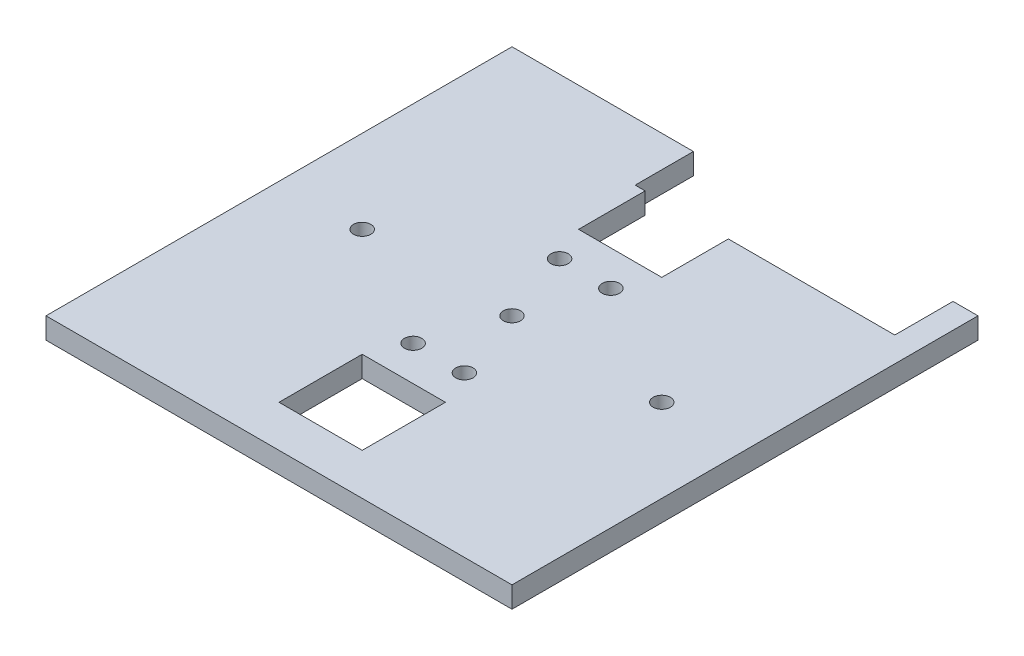
SolidWorks part; units mm, degrees
ref_plane "Front Plane" through (0, 0, 0) normal (0, 0, 1) x (1, 0, 0)
ref_plane "Top Plane" through (0, 0, 0) normal (0, 1, 0) x (1, 0, 0)
ref_plane "Right Plane" through (0, 0, 0) normal (1, 0, 0) x (0, 0, -1)
sketch "Sketch1" plane through (0, 0, 0) normal (0, 1, 0) x (1, 0, 0)
  line L1 (0, 0) -> (225, 0)
  line L2 (0, 0) -> (0, 225)
  line L3 (0, 225) -> (225, 225)
  line L4 (225, 0) -> (225, 225)
  line L5 (0, 0) -> (225, 225) construction
  line L6 (0, 225) -> (225, 0) construction
  point P4 (112.5, 112.5)
  dimension "D1" = 225
  dimension "D2" = 225
extrude "Boss-Extrude1" add sketch "Sketch1" along normal blind 6.35
sketch "Sketch2" plane through (0, 6.35, 0) normal (0, 1, 0) x (1, 0, 0)
  line L0 (222.5, 222.5) -> (222.5, 225) construction
  line L1 (2.5, 2.5) -> (222.5, 2.5) construction
  line L2 (2.5, 2.5) -> (2.5, 222.5) construction
  line L3 (2.5, 222.5) -> (222.5, 222.5) construction
  line L4 (222.5, 2.5) -> (222.5, 222.5) construction
  line L5 (112.5, 222.5) -> (112.5, 2.5) construction
  line L6 (2.5, 112.5) -> (222.5, 112.5) construction
  line L7 (225, 225) -> (0, 225) construction
  line L8 (222.5, 222.5) -> (225, 222.5) construction
  line L9 (225, 0) -> (225, 225) construction
  line L10 (2.5, 2.5) -> (0, 2.5) construction
  line L11 (0, 225) -> (0, 0) construction
  line L12 (2.5, 2.5) -> (2.5, 0) construction
  line L13 (0, 0) -> (225, 0) construction
  circle A0 centre (216.74, 216.74) radius 1.75
  circle A1 centre (8.26, 216.74) radius 1.75
  circle A2 centre (216.74, 8.26) radius 1.75
  circle A3 centre (8.26, 8.26) radius 1.75
  dimension "D2" = 5.76
  dimension "D4" = 3.5
  dimension "D1" = 220
  dimension "D3" = 5.76
extrude "Cut-Extrude1" cut sketch "Sketch2" against normal through all
sketch "Sketch3" plane through (0, 6.35, 0) normal (0, 1, 0) x (1, 0, 0)
  line L0 (112.5, 0) -> (112.5, 225) construction
  line L1 (0, 0) -> (225, 0) construction
  line L2 (225, 225) -> (0, 225) construction
  line L3 (225, 112.5) -> (0, 112.5) construction
  line L4 (225, 0) -> (225, 225) construction
  line L5 (0, 225) -> (0, 0) construction
  line L6 (125, 55) -> (100, 55)
  line L7 (175, 225) -> (97, 225)
  line L8 (175, 225) -> (175, 165)
  line L9 (175, 165) -> (97, 165)
  line L10 (97, 225) -> (97, 165)
  line L11 (125, 145) -> (100, 145)
  line L12 (125, 145) -> (125, 170)
  line L13 (125, 170) -> (100, 170)
  line L14 (100, 145) -> (100, 170)
  line L15 (100, 80) -> (100, 55)
  line L16 (125, 80) -> (100, 80)
  line L17 (125, 80) -> (125, 55)
  circle A0 centre (157.5, 112.5) radius 2.6
  circle A1 centre (112.5, 112.5) radius 2.6
  circle A2 centre (67.5, 112.5) radius 2.6
  circle A3 centre (120.2, 90.5) radius 2.6
  circle A4 centre (120.2, 134.5) radius 2.6
  circle A5 centre (104.8, 134.5) radius 2.6
  circle A6 centre (104.8, 90.5) radius 2.6
  point P31 (112.5, 145)
  line M13 (225, 225) -> (0, 225)
  dimension "D5" = 5.2
  dimension "D2" = 22
  dimension "D3" = 45
  dimension "D4" = 45
  dimension "D6" = 52.5
  dimension "D7" = 50
  dimension "D8" = 97
  dimension "D9" = 32.5
  dimension "D10" = 25
  dimension "D11" = 25
  dimension "D12" = 22
  dimension "D13" = 7.7
  dimension "D14" = 32.5
extrude "Cut-Extrude2" cut sketch "Sketch3" against normal up to surface (6.35 mm away) contours L14 L11 L12 L9 | L9 L14 L13 L12 L8 L10 M13 | A4 | A5 | A1 | A0 | A3 | A6 | A2 | L17 L16 L15 L6
sketch "Sketch4" plane through (0, 6.35, 0) normal (0, 1, 0) x (1, 0, 0)
  line L0 (112.5, 42.5) -> (112.5, 112.5) construction
  line L3 (182.5, 42.5) -> (42.5, 42.5)
  line L6 (182.5, 42.5) -> (182.5, 182.5)
  line L7 (182.5, 182.5) -> (42.5, 182.5)
  line L8 (42.5, 42.5) -> (42.5, 182.5)
  line L9 (112.5, 112.5) -> (42.5, 112.5) construction
  line L10 (112.5, 112.5) -> (112.5, 182.5) construction
  line L11 (112.5, 112.5) -> (182.5, 112.5) construction
  line L13 (225, 0) -> (0, 0)
  line L14 (225, 0) -> (225, 225)
  line L15 (225, 225) -> (0, 225)
  line L16 (0, 0) -> (0, 225)
  dimension "D1" = 140
extrude "Cut-Extrude3" cut sketch "Sketch4" against normal up to surface (6.35 mm away) up to face at (120.3333, 0, -154.1667)
